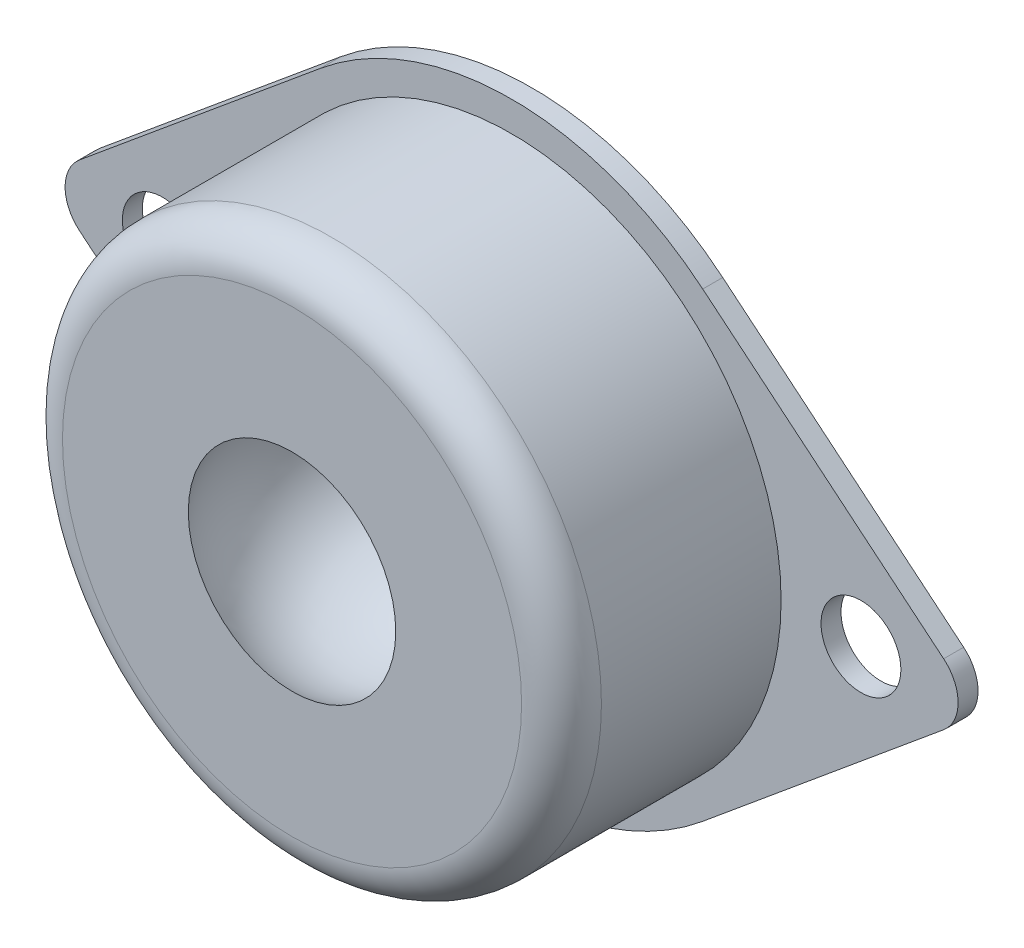
SolidWorks part; units mm, degrees
ref_plane "前视基准面" through (0, 0, 0) normal (0, 0, 1) x (1, 0, 0)
ref_plane "上视基准面" through (0, 0, 0) normal (0, 1, 0) x (1, 0, 0)
ref_plane "右视基准面" through (0, 0, 0) normal (1, 0, 0) x (0, 0, -1)
sketch "草图1" plane through (0, 0, 0) normal (0, 0, 1) x (1, 0, 0)
  line L0 (-23.5, 0) -> (23.5, 0) construction
  line L1 (0, 31.5658) -> (0, -35.7132) construction
  line L2 (-21.6433, 1.5396) -> (-9.5745, 11.5468)
  line L3 (-21.6433, -1.5396) -> (-9.5745, -11.5468)
  line L4 (21.6433, -1.5396) -> (9.5745, -11.5468)
  line L5 (21.6433, 1.5396) -> (9.5745, 11.5468)
  circle A0 centre (0, 0) radius 13.5
  circle A1 centre (-17.5, 0) radius 2
  circle A2 centre (17.5, 0) radius 2
  arc A3 (-21.6433, -1.5396) -> (-21.6433, 1.5396) centre (-20.3667, 0) cw
  arc A4 (21.6433, 1.5396) -> (21.6433, -1.5396) centre (20.3667, 0) cw
  arc A5 (-9.5745, 11.5468) -> (9.5745, 11.5468) centre (0, 0) cw
  arc A6 (-9.5745, -11.5468) -> (9.5745, -11.5468) centre (0, 0) ccw
  point P21 (-10.2808, 11.6578)
  point P23 (-9.5099, 11.5345)
  dimension "D1" = 27
  dimension "D4" = 2
  dimension "D5" = 2
  dimension "D6" = 4
  dimension "D7" = 15
  dimension "D2" = 47
  dimension "D3" = 35
extrude "凸台-拉伸3" add sketch "草图1" along normal blind 1 contours A3 L3 A0 L2 A1 | A4 L5 A0 L4 A2
sketch "草图3" plane through (0, 0, 0) normal (0, 0, 1) x (1, 0, 0)
  circle A0 centre (0, 0) radius 13.5
  dimension "D1" = 27
extrude "凸台-拉伸4" add sketch "草图3" along normal blind 12
fillet "圆角3" radius 2 1 edges at (13.5, 0, 12)
sketch "草图4" plane through (0, 0, 0) normal (0, 1, 0) x (1, 0, 0)
  line L1 (0, 0) -> (0, -18.0744) construction
  line L2 (0, -3) -> (0, -15) construction
  line L3 (0, -12) -> (5.1962, -12)
  line L4 (-11.5, -12) -> (11.5, -12) construction
  line L5 (0, -12) -> (0, -3)
  line L6 (9.5745, 0) -> (-9.5745, 0) construction
  circle A0 centre (0, -9) radius 6 construction
  arc A1 (0, -3) -> (0, -15) centre (0, -9) cw construction
  arc A2 (0, -3) -> (5.1962, -12) centre (0, -9) cw
  dimension "D2" = 12
  dimension "D1" = 9
revolve "切除-旋转9" cut sketch "草图4" angle 360 about L1
